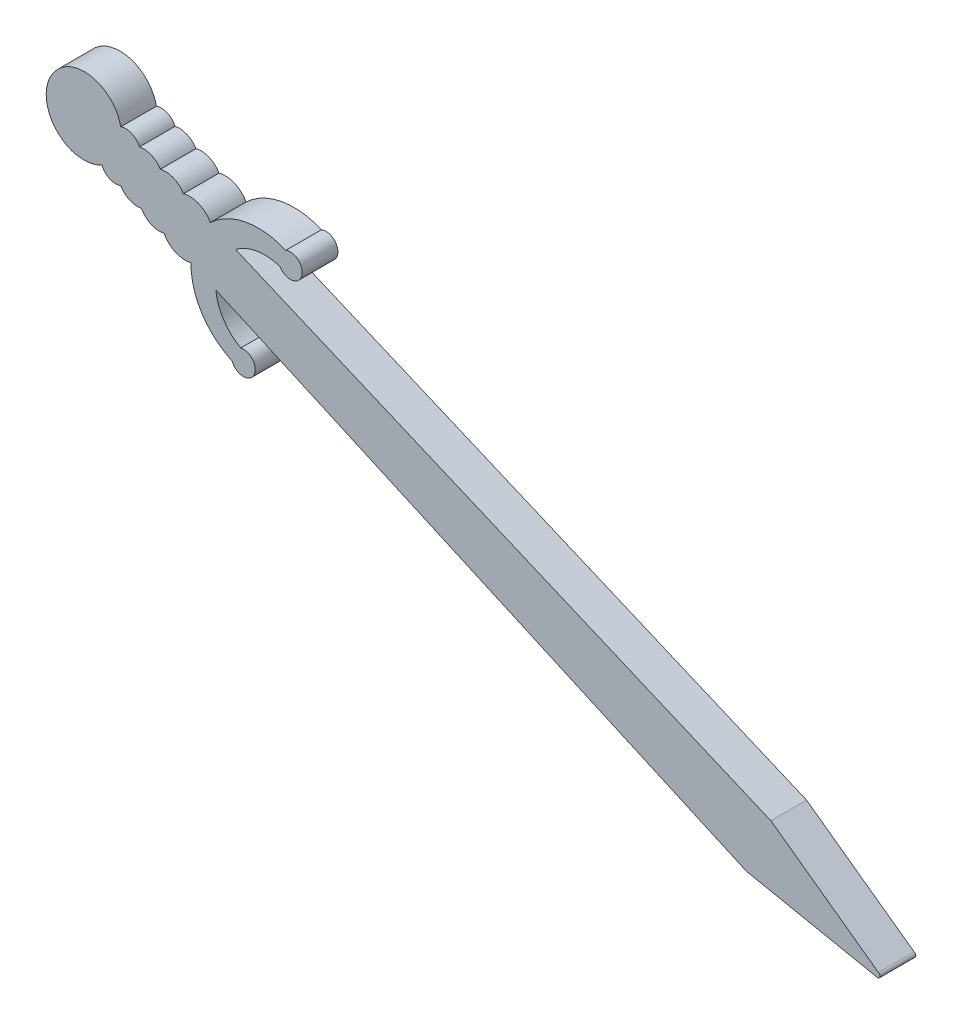
SolidWorks part; units mm, degrees
ref_plane "Alzado" through (0, 0, 0) normal (0, 0, 1) x (1, 0, 0)
ref_plane "Planta" through (0, 0, 0) normal (0, 1, 0) x (1, 0, 0)
ref_plane "Vista lateral" through (0, 0, 0) normal (1, 0, 0) x (0, 0, -1)
sketch "Model" plane through (0, 0, 0) normal (0, 0, 1) x (1, 0, 0)
  line L0 (66.714, 2.6754) -> (68.5381, 2.3067)
  line L1 (12.9786, 24.5443) -> (16.5464, 22.9427)
  line L2 (16.5464, 22.9427) -> (57.5858, 4.5202)
  line L3 (57.5858, 4.5202) -> (66.714, 2.6754)
  line L4 (14.6289, 28.3254) -> (18.2292, 26.7984)
  line L5 (18.2292, 26.7984) -> (59.6428, 9.233)
  line L6 (59.6428, 9.233) -> (68.6938, 2.7017)
  arc A0 (10.2421, 30.1861) -> (8.3105, 31.0053) centre (8.7357, 29.3212) ccw
  arc A1 (8.3105, 31.0053) -> (6.5511, 31.7516) centre (6.8958, 30.117) ccw
  arc A2 (6.5511, 31.7516) -> (4.9803, 32.4348) centre (5.3941, 31.2387) ccw
  arc A3 (12.5142, 29.2224) -> (10.2421, 30.1861) centre (10.7726, 28.2765) ccw
  arc A4 (18.8569, 30.3748) -> (12.5142, 29.2224) centre (16.5615, 24.9776) ccw
  arc A5 (8.6314, 26.4957) -> (10.883, 25.485) centre (10.3923, 27.4052) ccw
  arc A6 (6.7173, 27.355) -> (8.6314, 26.4957) centre (8.2413, 28.1884) ccw
  arc A7 (4.9738, 28.1376) -> (6.7173, 27.355) centre (6.4067, 28.9963) ccw
  arc A8 (3.3956, 28.8461) -> (4.9738, 28.1376) centre (4.5631, 29.3348) ccw
  arc A9 (1.4838, 28.4963) -> (3.3956, 28.8461) centre (1.894, 31.6534) ccw
  arc A10 (10.883, 25.485) -> (14.3507, 20.0506) centre (16.7474, 25.4036) ccw
  arc A11 (0.0625, 29.0492) -> (1.4838, 28.4963) centre (1.6977, 31.1491) ccw
  arc A12 (-0.6913, 33.5115) -> (0.0625, 29.0492) centre (1.894, 31.6534) ccw
  arc A13 (4.9803, 32.4348) -> (-0.6913, 33.5115) centre (1.9191, 31.7856) ccw
  arc A14 (68.5381, 2.3067) -> (68.6938, 2.7017) centre (68.6159, 2.5042) ccw
  arc A15 (18.3759, 28.9462) -> (18.8569, 30.3748) centre (19.2392, 29.4508) ccw
  arc A16 (18.3759, 28.9462) -> (14.6289, 28.3254) centre (17.0882, 25.0997) ccw
  arc A17 (14.3507, 20.0506) -> (15.0712, 21.3747) centre (15.2882, 20.3986) ccw
  arc A18 (12.9786, 24.5443) -> (15.0712, 21.3747) centre (17.016, 24.9343) ccw
extrude "Saliente-Extruir1" add sketch "Model" along normal blind 3
